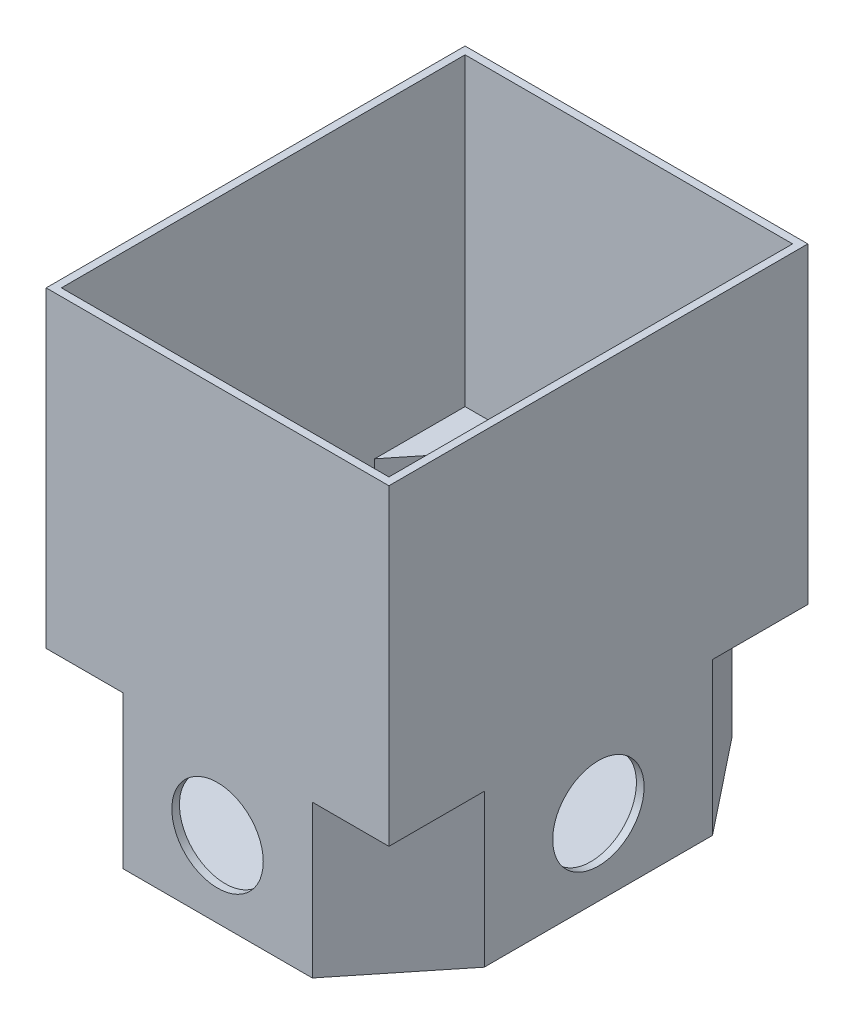
SolidWorks part; units mm, degrees
other "Markup1"
sketch "Sketch5" plane through (-59.5584, 0, 51.6967) normal (0, -1, 0) x (0, 0, -1)
ref_plane "Front Plane" through (0, 0, 0) normal (0, 0, 1) x (1, 0, 0)
ref_plane "Top Plane" through (0, 0, 0) normal (0, 1, 0) x (1, 0, 0)
ref_plane "Right Plane" through (0, 0, 0) normal (1, 0, 0) x (0, 0, -1)
sketch "Sketch1" plane through (0, 0, 0) normal (0, 1, 0) x (1, 0, 0)
  line L1 (-59.5584, 58.3033) -> (30.4416, 58.3033)
  line L2 (-59.5584, 58.3033) -> (-59.5584, -51.6967)
  line L3 (-59.5584, -51.6967) -> (30.4416, -51.6967)
  line L4 (30.4416, 58.3033) -> (30.4416, -51.6967)
extrude "Boss-Extrude1" add sketch "Sketch1" along normal blind 82
sketch3d "3DSketch1"
  line L0 (28.4416, 82, 49.6967) -> (28.4416, 82, -56.3033)
  line L1 (28.4416, 82, -56.3033) -> (-57.5584, 82, -56.3033)
  line L2 (-57.5584, 82, -56.3033) -> (-57.5584, 82, 49.6967)
  line L3 (-57.5584, 82, 49.6967) -> (28.4416, 82, 49.6967)
  line L4 (28.4416, 82, 49.6967) -> (28.4416, 82, -56.3033)
  line L5 (28.4416, 82, -56.3033) -> (-57.5584, 82, -56.3033)
  line L6 (-57.5584, 82, -56.3033) -> (-57.5584, 82, 49.6967)
  line L7 (-57.5584, 82, 49.6967) -> (28.4416, 82, 49.6967)
  dimension "D1" = 2
extrude "Cut-Extrude1" cut sketch "3DSketch1" along direction (0, 1, 0) on the side against the normal blind 80
sketch "Sketch7" plane through (0, 0, 0) normal (0, -1, 0) x (1, 0, 0)
  line L0 (30.4416, 26.6605) -> (30.4416, -33.2671)
  line L3 (30.4416, 51.6967) -> (30.4416, -58.3033) construction
  line L4 (-39.4395, -58.3033) -> (10.5605, -58.3033)
  line L5 (30.4416, -58.3033) -> (-59.5584, -58.3033) construction
  line L6 (10.3226, 51.6967) -> (-39.4395, 51.6967)
  line L7 (-59.5584, 51.6967) -> (30.4416, 51.6967) construction
  line L8 (-59.5584, 26.6605) -> (-59.5584, -33.2671)
  line L9 (-59.5584, -58.3033) -> (-59.5584, 51.6967) construction
  line L10 (-59.5584, -33.2671) -> (-39.4395, -58.3033)
  line L11 (10.5605, -58.3033) -> (30.4416, -33.2671)
  line L12 (30.4416, 26.6605) -> (10.3226, 51.6967)
  line L13 (-39.4395, 51.6967) -> (-59.5584, 26.6605)
  point P5 (30.4416, -3.3033)
  point P10 (-14.4395, -58.3033)
  point P15 (-14.5584, 51.6967)
  point P20 (-59.5584, -3.3033)
extrude "Boss-Extrude2" add sketch "Sketch7" along normal blind 40 contours L12 L6 L13 L8 L10 L4 L11 L0
sketch "Sketch10" plane through (0, 2, 0) normal (0, 1, 0) x (1, 0, 0)
  line L16 (28.4416, -25.9565) -> (28.4416, 32.5696)
  line L17 (9.3641, -49.6967) -> (28.4416, -25.9565)
  line L18 (-38.4809, -49.6967) -> (9.3641, -49.6967)
  line L19 (-57.5584, -25.9565) -> (-38.4809, -49.6967)
  line L20 (-57.5584, 32.5631) -> (-57.5584, -25.9565)
  line L21 (-38.4809, 56.3033) -> (-57.5584, 32.5631)
  line L22 (9.5948, 56.3033) -> (-38.4809, 56.3033)
  line L23 (28.4416, 32.5696) -> (9.5948, 56.3033)
  line L24 (28.4416, -25.9565) -> (28.4416, 32.5696)
  line L25 (9.3641, -49.6967) -> (28.4416, -25.9565)
  line L26 (-38.4809, -49.6967) -> (9.3641, -49.6967)
  line L27 (-57.5584, -25.9565) -> (-38.4809, -49.6967)
  line L28 (-57.5584, 32.5631) -> (-57.5584, -25.9565)
  line L29 (-38.4809, 56.3033) -> (-57.5584, 32.5631)
  line L30 (9.5948, 56.3033) -> (-38.4809, 56.3033)
  line L31 (28.4416, 32.5696) -> (9.5948, 56.3033)
  dimension "D1" = 2
extrude "Cut-Extrude2" cut sketch "Sketch10" against normal blind 40
sketch "Sketch11" plane through (30.4416, 0, 0) normal (1, 0, 0) x (0, 0, -1)
  circle A0 centre (3.3033, -20) radius 12
  dimension "D1" = 24
extrude "Cut-Extrude3" cut sketch "Sketch11" against normal blind 94
sketch "Sketch12" plane through (0, 0, 51.6967) normal (0, 0, 1) x (1, 0, 0)
  circle A0 centre (-14.5584, -20) radius 12.0033
extrude "Cut-Extrude4" cut sketch "Sketch12" against normal blind 113
